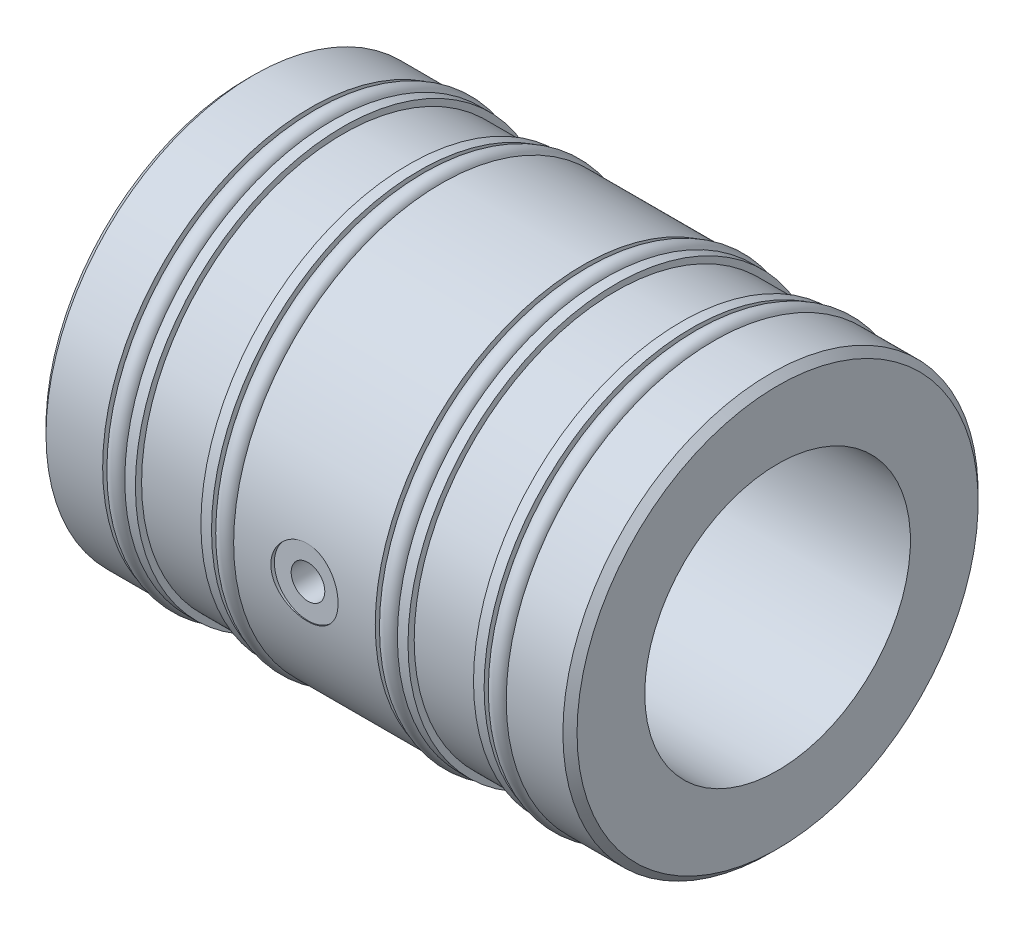
SolidWorks part; units mm, degrees
ref_plane "Front Plane" through (0, 0, 0) normal (0, 0, 1) x (1, 0, 0)
ref_plane "Top Plane" through (0, 0, 0) normal (0, 1, 0) x (1, 0, 0)
ref_plane "Right Plane" through (0, 0, 0) normal (1, 0, 0) x (0, 0, -1)
sketch "Sketch1" plane through (0, 0, 0) normal (0, 0, 1) x (1, 0, 0)
  line L0 (0, 19.0602) -> (76.2, 19.0602)
  line L1 (76.2, 19.0602) -> (76.2, 29.7942)
  line L2 (76.2, 29.7942) -> (67.056, 29.7942)
  line L3 (67.056, 29.7942) -> (67.056, 27.813)
  line L4 (67.056, 27.813) -> (63.881, 27.813)
  line L5 (63.881, 27.813) -> (63.881, 29.7942)
  line L6 (63.881, 29.7942) -> (62.357, 29.7942)
  line L7 (62.357, 29.7942) -> (62.357, 28.9052)
  line L8 (0, 19.0602) -> (0, 29.7942)
  line L9 (0, 29.7942) -> (9.144, 29.7942)
  line L10 (9.144, 29.7942) -> (9.144, 27.813)
  line L11 (9.144, 27.813) -> (12.319, 27.813)
  line L12 (12.319, 27.813) -> (12.319, 29.7942)
  line L13 (12.319, 29.7942) -> (13.843, 29.7942)
  line L14 (13.843, 29.7942) -> (13.843, 28.9052)
  line L15 (13.843, 28.9052) -> (23.241, 28.9052)
  line L16 (23.241, 28.9052) -> (23.241, 29.7942)
  line L17 (23.241, 29.7942) -> (24.765, 29.7942)
  line L18 (24.765, 29.7942) -> (24.765, 27.813)
  line L19 (24.765, 27.813) -> (27.94, 27.813)
  line L20 (27.94, 27.813) -> (27.94, 29.7942)
  line L21 (27.94, 29.7942) -> (48.26, 29.7942)
  line L22 (48.26, 29.7942) -> (48.26, 27.813)
  line L23 (62.357, 28.9052) -> (52.959, 28.9052)
  line L24 (52.959, 28.9052) -> (52.959, 29.7942)
  line L25 (52.959, 29.7942) -> (51.435, 29.7942)
  line L26 (51.435, 29.7942) -> (51.435, 27.813)
  line L27 (51.435, 27.813) -> (48.26, 27.813)
  line L28 (0, 0) -> (76.2, 0) construction
  dimension "Bore ID" = 38.1203
  dimension "OAL" = 76.2
  dimension "Moglice groove width" = 9.398
  dimension "O-ring groove width" = 3.175
  dimension "Edge to 1st o-ring groove" = 9.144
  dimension "Edge to 2nd o-ring groove" = 24.765
  dimension "Bushing OD" = 59.5884
  dimension "O-ring groove dia" = 55.626
  dimension "Edge to 3rd o-ring groove" = 48.26
  dimension "edge to 4th o-ring groove" = 63.881
  dimension "Edge to 1st moglice groove" = 13.843
  dimension "Edge to 2nd moglice groove" = 52.959
  dimension "Moglice Groove Dia" = 57.8104
revolve "Revolve1" add sketch "Sketch1" angle 360 about L28
chamfer "Chamfer1" distance 1.016 angle 45 2 edges at (0, 0, 29.7942) (76.2, 0, 29.7942)
ref_plane "Plane1" through (0, 0, -7.9121) normal (0, 0, 1) x (1, 0, 0)
hole_wizard "1/4 (0.25) Diameter Hole1" positions "3DSketch1" profile "Sketch2" hole size "1/4" standard "Ansi Inch"
sketch3d "3DSketch1"
  point P0 (38.1, 0, 29.7942)
  dimension "Edge to air hole" = 38.1
sketch "Sketch2" plane through (38.1, 0, 29.7942) normal (1, 0, 0) x (0, -1, 0)
  line L0 (0, 0) -> (0, 0.508)
  line L1 (0, 0.508) -> (4.826, 0.508)
  line L2 (4.826, 0.508) -> (4.826, 0)
  line L5 (4.826, 0) -> (0, 0)
  line L10 (0, 0.508) -> (-4.826, 0.508) construction
  line L11 (0, -6.35) -> (0, 107.95) construction
  dimension "Hole Dia." = 9.652
  dimension "Hole Depth" = 0.508
  dimension "Drill Angle" = 180
hole_wizard "Air Hole" positions "Sketch4" profile "Sketch3" tap size "M3x0.5" standard "Ansi Metric"
sketch "Sketch4" plane through (0, 0, 29.2862) normal (0, 0, 1) x (1, 0, 0)
  circle A0 centre (38.1, 0) radius 4.826 construction
  point P0 (38.1, 0)
sketch "Sketch3" plane through (38.1, 0, 29.2862) normal (1, 0, 0) x (0, -1, 0)
  line L0 (0, 0) -> (0, 7.5786)
  line L1 (0, 7.5786) -> (2.0447, 6.35)
  line L2 (2.0447, 6.35) -> (2.0447, 5.9944)
  line L3 (2.0447, 5.9944) -> (2.413, 5.9944)
  line L4 (2.413, 5.9944) -> (2.413, 0)
  line L5 (2.413, 0) -> (0, 0)
  line L10 (0, 7.5786) -> (-2.0447, 6.35) construction
  line L11 (0, -6.35) -> (0, 107.95) construction
  dimension "Tap Drill Dia." = 4.0894
  dimension "Tap Drill Depth" = 6.35
  dimension "Thread Major Dia." = 4.826
  dimension "Thread Depth" = 5.9944
  dimension "Drill Angle" = 118
sketch "Sketch5" plane through (0, 0, 0) normal (0, 0, 1) x (1, 0, 0)
  line L0 (0, 0) -> (76.2, 0) construction
  line L1 (9.144, 29.7942) -> (9.144, 27.813) construction
  line L2 (24.765, 29.7942) -> (24.765, 27.813) construction
  line L3 (48.26, 29.7942) -> (48.26, 27.813) construction
  line L4 (63.881, 27.813) -> (63.881, 29.7942) construction
  circle A0 centre (10.7315, 28.9306) radius 1.3081
  circle A1 centre (26.3525, 28.9306) radius 1.3081
  circle A2 centre (49.8475, 28.9306) radius 1.3081
  circle A3 centre (65.4685, 28.9306) radius 1.3081
  dimension "D1" = 2.6162
  dimension "D2" = 30.2387
  dimension "D3" = 1.5875
  dimension "D4" = 1.5875
  dimension "D5" = 1.5875
  dimension "D6" = 1.5875
revolve "Revolve2" add sketch "Sketch5" angle 360 about L28
equation "\"plane offset\"= \"Bushing OD@Sketch1\" / 2"
